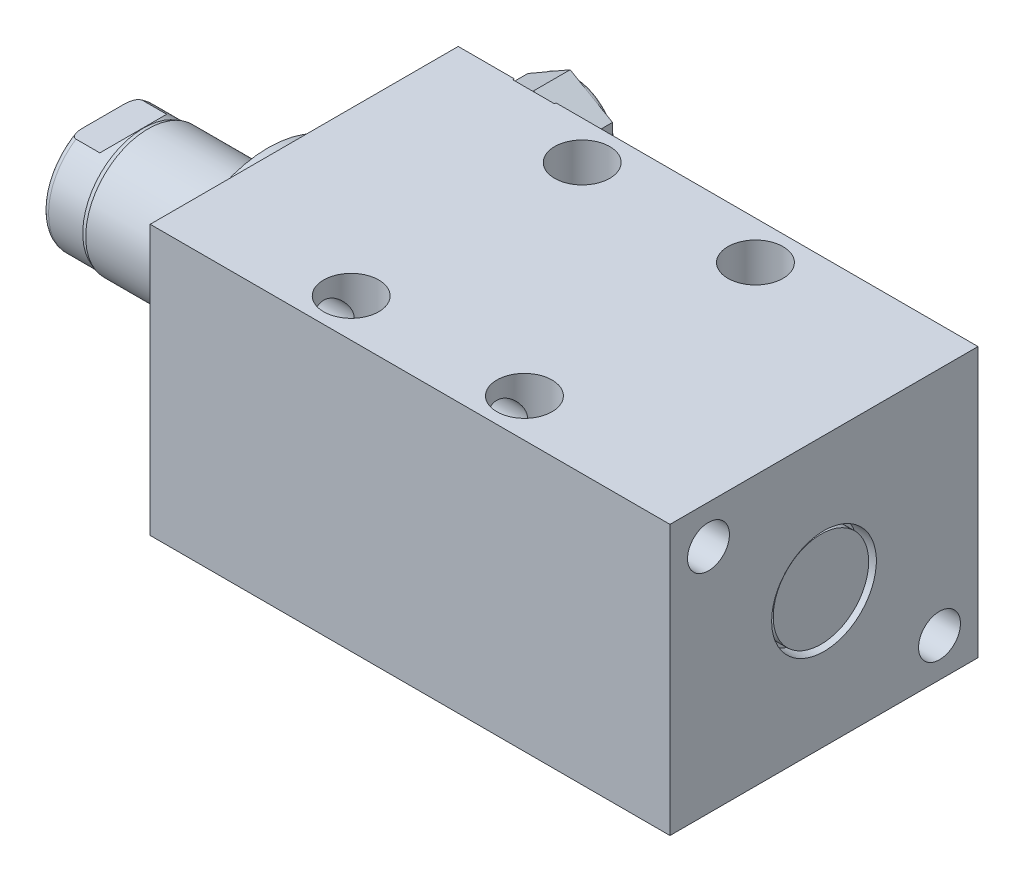
SolidWorks part; units mm, degrees
material "Alloy Steel"
ref_plane "Front Plane" through (0, 0, 0) normal (0, 0, 1) x (1, 0, 0)
ref_plane "Top Plane" through (0, 0, 0) normal (0, 1, 0) x (1, 0, 0)
ref_plane "Right Plane" through (0, 0, 0) normal (1, 0, 0) x (0, 0, -1)
ref_plane "Plane1" through (0, 0, 0) normal (1, 0, 0) x (0, 0, -1)
sketch "Sketch1" plane through (0, 0, 0) normal (1, 0, 0) x (0, 0, -1)
  line L0 (-25.4, 22.225) -> (25.4, 22.225)
  line L1 (25.4, 22.225) -> (25.4, -22.225)
  line L2 (25.4, -22.225) -> (-25.4, -22.225)
  line L3 (-25.4, -22.225) -> (-25.4, 22.225)
  line L4 (0, -24.4475) -> (0, 24.4475) construction
  dimension "D1" = 44.45
  dimension "D2" = 22.225
  dimension "D3" = 50.8
  dimension "D4" = 25.4
extrude "Extrude1" add sketch "Sketch1" along normal blind 85.725
ref_plane "Plane12" through (0, 14.3, 0) normal (0, 1, 0) x (-1, 0, 0)
sketch "S2D0002" plane through (0, 14.3, 0) normal (0, 1, 0) x (-1, 0, 0)
  line L0 (-17.7165, -25.146) -> (-21.336, -25.146)
  line L1 (-17.7165, -25.1206) -> (-17.7165, -25.146)
  line L2 (-17.7165, -25.1206) -> (-17.1196, -24.5237)
  line L3 (-17.1196, -24.5237) -> (-17.1196, -11.684)
  line L4 (-17.1196, -11.684) -> (-12.7, -11.684)
  line L5 (-12.7, -11.684) -> (-12.7, -25.4)
  line L6 (-12.7, -19.1384) -> (-12.7, 0.6985) construction
  line L7 (0, -25.4) -> (0, 25.4) construction
  line L8 (-21.336, -25.4) -> (-21.336, -25.146)
  line L9 (-85.725, -25.4) -> (0, -25.4) construction
  line L10 (-21.336, -25.4) -> (-12.7, -25.4)
  dimension "D1" = 13.716
  dimension "D2" = 12.7
  dimension "D3" = 8.8392
  dimension "D4" = 45
  dimension "D5" = 0.6223
  dimension "D6" = 10.033
  dimension "D7" = 0.0254
  dimension "D8" = 0.254
  dimension "D9" = 17.272
revolve "Cut-Revolve1" cut sketch "S2D0002" angle 360 about L6
pattern_linear "LPattern1" count 2 spacing 57.15 along (1, 0, 0) count 2 spacing 14.3 along (0, -1, 0) skipping (0, 1), (1, 0) of "Cut-Revolve1"
sketch "Sketch5" plane through (0, 0, 0) normal (-1, 0, 0) x (0, 0, 1)
  circle A0 centre (0, 0) radius 17.4625
  dimension "D1" = 34.925
extrude "Extrude2" add sketch "Sketch5" along normal blind 5.969
ref_plane "Plane5" through (0, 0, 0) normal (0, -1, 0) x (0, 0, 1)
sketch "Sketch6" plane through (0, 0, 0) normal (0, -1, 0) x (0, 0, 1)
  line L0 (0, 5.969) -> (-10.306, 5.969)
  line L1 (-10.306, 5.969) -> (-10.306, 33.147)
  line L2 (-10.306, 33.147) -> (0, 33.147)
  line L3 (0, 33.147) -> (0, 5.969)
  line L4 (0, -5.7546) -> (0, 21.1709) construction
  line L5 (17.4625, 5.969) -> (-17.4625, 5.969) construction
  line L6 (25.4, -85.725) -> (-25.4, -85.725) construction
  dimension "D1" = 118.872
  dimension "D2" = 20.6121
revolve "Revolve1" add sketch "Sketch6" angle 360 about L4
ref_plane "Plane6" through (-18.5113, 3.2639, 0) normal (0, 0, 1) x (0, 1, 0)
sketch "S2D0001" plane through (-18.5113, 3.2639, 0) normal (0, 0, 1) x (0, 1, 0)
  line L0 (0.1271, 12.9201) -> (0.1271, -0.3043)
  line L1 (-3.2639, -0.3043) -> (0.1271, -0.3043)
  line L2 (1.1176, 14.6357) -> (-3.2639, 14.6357)
  line L3 (-3.2639, 14.6357) -> (-3.2639, -0.3043)
  line L4 (0.1271, 12.9201) -> (1.1176, 14.6357)
  line L5 (-3.2639, -18.5113) -> (-3.2639, 2.765) construction
  line L6 (7.0421, 14.6357) -> (-13.5699, 14.6357) construction
  dimension "D1" = 30
  dimension "D2" = 8.763
  dimension "D3" = 6.782
  dimension "D4" = 14.94
  dimension "D5" = 90
revolve "Cut-Revolve4" cut sketch "S2D0001" angle 360 about L5
ref_plane "Plane7" through (0, 0, 0) normal (0, 1, 0) x (0, 0, -1)
sketch "Sketch8" plane through (0, 0, 0) normal (0, 1, 0) x (0, 0, -1)
  line L0 (-10.306, 25.73) -> (-10.033, 26.492)
  line L1 (-10.033, 26.492) -> (-10.033, 32.131)
  line L2 (0, 12.6594) -> (0, 20.8178) construction
  line L3 (-10.306, 25.73) -> (-10.306, 33.147)
  line L4 (-9.017, 33.147) -> (-10.306, 33.147)
  line L5 (10.306, 33.147) -> (-10.306, 33.147) construction
  line L6 (-10.306, 33.147) -> (-10.306, 5.969) construction
  arc A0 (-9.017, 33.147) -> (-10.033, 32.131) centre (-9.017, 32.131) ccw
  dimension "D2" = 1.016
  dimension "D1" = 20.066
  dimension "D3" = 1.016
  dimension "D4" = 0.762
  dimension "D5" = 6.655
revolve "Cut-Revolve5" cut sketch "Sketch8" angle 360 about L2
ref_plane "Plane11" through (0, 0, 0) normal (0, 0, -1) x (0, -1, 0)
sketch "Sketch12" plane through (0, 0, 0) normal (0, 0, -1) x (0, -1, 0)
  line L0 (8.382, 33.147) -> (8.382, 28.194)
  line L1 (8.382, 28.194) -> (10.033, 26.543)
  line L2 (-8.382, 33.147) -> (-8.382, 28.194)
  line L3 (-8.382, 28.194) -> (-10.033, 26.543)
  line L4 (8.382, 33.147) -> (10.033, 33.147)
  line L5 (0, 13.7262) -> (0, 20.767) construction
  line L6 (-10.033, 26.543) -> (-10.033, 33.147)
  line L8 (10.033, 26.492) -> (10.033, 32.131) construction
  line L9 (10.033, 26.543) -> (10.033, 33.147)
  line L10 (-8.382, 33.147) -> (-10.033, 33.147)
  line L12 (9.017, 33.147) -> (-9.017, 33.147) construction
  dimension "D1" = 16.764
  dimension "D2" = 4.953
  dimension "D3" = 45
extrude "Cut-Extrude4" cut sketch "Sketch12" against normal mid plane 60.96
hole_wizard "Hole1" positions "Sketch15" profile "Sketch14" legacy end condition up to next
sketch "Sketch15" plane through (0, 0, 0) normal (-1, 0, 0) x (0, 0, 1)
  line L0 (0, 0) -> (-29.9914, 0) construction
  line L1 (0, 0) -> (0, 25.7648) construction
  point P0 (-19.05, -15.875)
  point P11 (19.05, 15.875)
  dimension "D1" = 15.875
  dimension "D2" = 19.05
  dimension "D3" = 31.75
  dimension "D4" = 38.1
sketch "Sketch14" plane through (0, -15.875, -19.05) normal (0, 1, 0) x (0, 0, 1)
  line L0 (0, 0) -> (0, 85.725)
  line L1 (0, 85.725) -> (3.4545, 85.725)
  line L2 (3.4545, 85.725) -> (3.4545, 0)
  line L3 (3.4545, 0) -> (0, 0)
  line L4 (0, 110) -> (0, -10) construction
  dimension "Diameter" = 6.909
  dimension "Depth" = 85.725
hole_wizard "Hole2" positions "Sketch17" profile "Sketch16" legacy
sketch "Sketch17" plane through (0, 22.225, 0) normal (0, 1, 0) x (-1, 0, 0)
  line L0 (0, 0) -> (-59.3363, 0) construction
  line L1 (0, -25.4) -> (0, 25.4) construction
  point P0 (-26.797, -19.05)
  point P9 (-26.797, 19.05)
  dimension "D1" = 38.1
  dimension "D2" = 26.797
  dimension "D3" = 19.05
sketch "Sketch16" plane through (26.797, 22.225, -19.05) normal (1, 0, 0) x (0, 0, 1)
  line L0 (0, 0) -> (0, 44.45)
  line L1 (0, 44.45) -> (4.5465, 44.45)
  line L2 (4.5465, 44.45) -> (4.5465, 0)
  line L3 (4.5465, 0) -> (0, 0)
  line L4 (0, 110) -> (0, -10) construction
  dimension "Diameter" = 9.093
  dimension "Depth" = 44.45
sketch "Sketch18" plane through (0, 0, -25.146) normal (0, 0, -1) x (-1, 0, 0)
  line L1 (-5.715, 18.3328) -> (-12.7, 22.3656)
  line L2 (-12.7, 22.3656) -> (-19.685, 18.3328)
  line L3 (-19.685, 18.3328) -> (-19.685, 10.2672)
  line L4 (-19.685, 10.2672) -> (-12.7, 6.2344)
  line L5 (-12.7, 6.2344) -> (-5.715, 10.2672)
  line L6 (-5.715, 10.2672) -> (-5.715, 18.3328)
  circle A0 centre (-12.7, 14.3) radius 6.985 construction
  dimension "D1" = 13.97
extrude "Extrude3" add sketch "Sketch18" along normal blind 6.78
sketch "Sketch19" plane through (0, 14.3, 0) normal (0, 1, 0) x (-1, 0, 0)
  line L0 (-12.7, -18.5103) -> (-12.7, -44.3941) construction
  line L1 (-12.7, -11.684) -> (-12.7, -24.5237) construction
  line L2 (-12.7, -31.926) -> (-19.685, -31.926) construction
  line L3 (-19.685, -31.926) -> (-19.685, -25.146) construction
  line L4 (-18.923, -31.926) -> (-18.923, -34.339)
  line L5 (-18.923, -34.339) -> (-22.098, -34.339)
  line L6 (-22.098, -34.339) -> (-22.098, -31.164)
  line L7 (-22.098, -31.164) -> (-19.685, -31.164)
  arc A0 (-19.685, -31.164) -> (-18.923, -31.926) centre (-18.923, -31.164) ccw
  dimension "D1" = 0.762
  dimension "D2" = 3.175
  dimension "D3" = 3.175
revolve "Cut-Revolve6" cut sketch "Sketch19" angle 360 about L0
sketch "Sketch20" plane through (0, 0, 0) normal (0, 1, 0) x (1, 0, 0)
  line L0 (0, 0) -> (70.5114, 0) construction
  line L1 (85.725, 8.636) -> (82.677, 8.636)
  line L2 (85.725, 25.4) -> (85.725, -25.4) construction
  line L3 (82.677, 8.636) -> (82.677, 5.0165)
  line L4 (82.677, 5.0165) -> (82.6516, 5.0165)
  line L5 (82.6516, 5.0165) -> (82.0547, 4.4196)
  line L6 (82.0547, 4.4196) -> (72.1106, 4.4196)
  line L7 (72.1106, 4.4196) -> (72.1106, 0)
  line L8 (72.1106, 0) -> (85.725, 0)
  line L9 (85.725, 0) -> (85.725, 8.636)
  dimension "D1" = 17.272
  dimension "D2" = 3.048
  dimension "D3" = 10.033
  dimension "D4" = 0.0254
  dimension "D5" = 45
  dimension "D6" = 8.8392
  dimension "D7" = 10.5664
revolve "Cut-Revolve7" cut sketch "Sketch20" angle 360 about L0
sketch "Sketch21" plane through (82.677, 0, 0) normal (1, 0, 0) x (0, 0, -1)
  circle A0 centre (0, 0) radius 7.874
  dimension "D1" = 15.748
extrude "Extrude4" add sketch "Sketch21" along normal blind 2.54
pattern_linear "LPattern2" count 2 spacing 28.575 along (1, 0, 0) of "Hole2"
